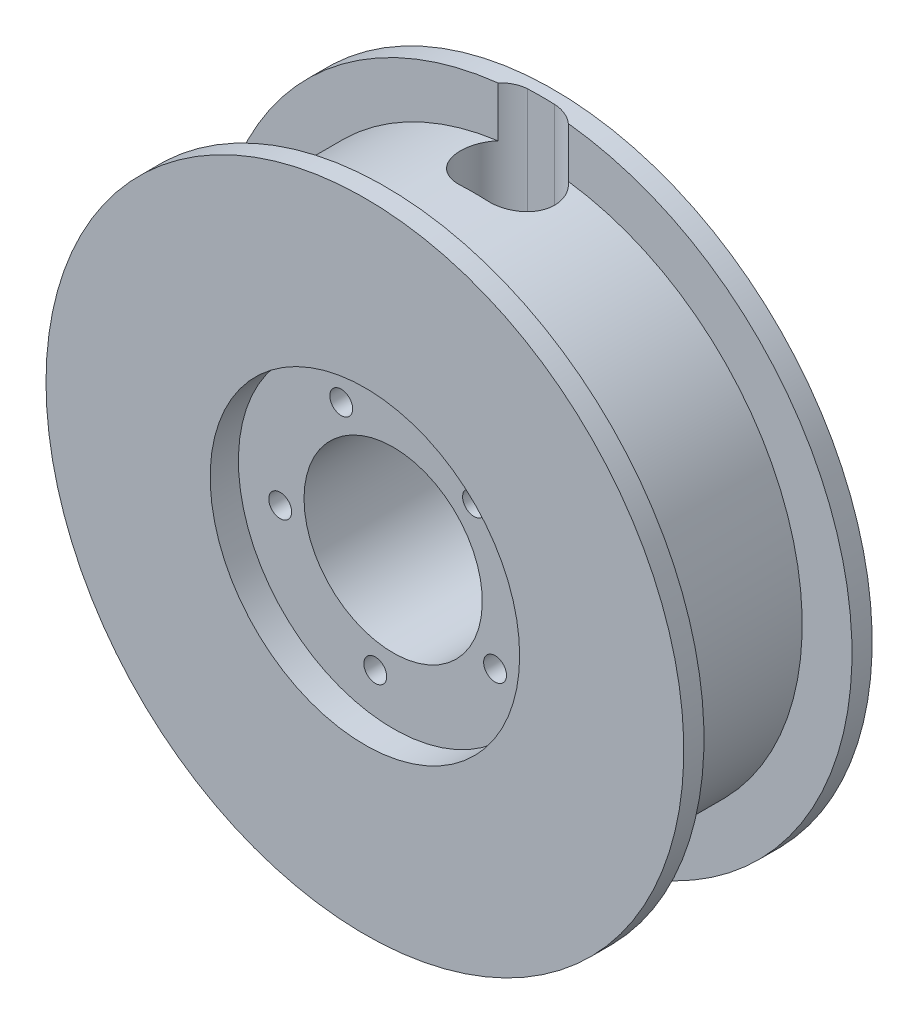
SolidWorks part; units mm, degrees
ref_plane "Ebene vorne" through (0, 0, 0) normal (0, 0, 1) x (1, 0, 0)
ref_plane "Ebene oben" through (0, 0, 0) normal (0, 1, 0) x (1, 0, 0)
ref_plane "Ebene rechts" through (0, 0, 0) normal (1, 0, 0) x (0, 0, -1)
sketch "Skizze3" plane through (0, 0, 0) normal (1, 0, 0) x (0, 0, -1)
  line L0 (-1.5, 4.2) -> (0, 4.2)
  line L1 (0, 4.2) -> (0, 0.5)
  line L2 (0, 0.5) -> (11, 0.5)
  line L3 (5.5, 0.5) -> (5.5, -39) construction
  line L4 (0, -39) -> (11, -39) construction
  line L5 (-1.5, 4.2) -> (-1.5, -12.875)
  line L6 (-1.5, -12.875) -> (12.5, -12.875)
  line L7 (12.5, 4.2) -> (12.5, -12.875)
  line L8 (11, 4.2) -> (11, 0.5)
  line L9 (12.5, 4.2) -> (11, 4.2)
  line L10 (11, 0) -> (0, 0) construction
  line L11 (13, -19.5) -> (-2, -19.5) construction
  line L12 (13, -47) -> (13, 8) construction
  line L13 (-2, 8) -> (-2, -47) construction
  line L14 (7.6, -13.375) -> (0.1, -13.375) construction
  point P10 (5.5, -12.875)
  dimension "D1" = 1.5
  dimension "D2" = 0.5
  dimension "D3" = 0.5
revolve "Rotation1" add sketch "Skizze3" angle 360 about L11
sketch "Skizze4" plane through (0, 0, 1.5) normal (0, 0, 1) x (1, 0, 0)
  circle A0 centre (0, -19.5) radius 11.5
  circle A1 centre (0, -19.5) radius 11 construction
  dimension "D1" = 0.5
extrude "Schnitt-Linear austragen1" cut sketch "Skizze4" against normal offset from surface (2.1 mm away) 0.5
sketch "Skizze5" plane through (0, 0, 1.5) normal (0, 0, 1) x (1, 0, 0)
  circle A0 centre (6.0104, -13.4896) radius 1
  circle A1 centre (7.5736, -23.3589) radius 1
  circle A2 centre (-1.3297, -27.8954) radius 1
  circle A3 centre (-8.3954, -20.8297) radius 1
  circle A4 centre (-3.8589, -11.9264) radius 1
  point P13 (0, -19.5)
  dimension "D2" = 2
  dimension "D1" = 5
extrude "Schnitt-Linear austragen2" cut sketch "Skizze5" against normal blind 1 from surface at -8
sketch "Skizze6" plane through (9.0133, -13.375, -16.4366) normal (0, 1, 0) x (1, 0, 0)
  line L0 (-10.0133, -7.3366) -> (-8.0133, -7.3366) construction
  line L1 (-10.0133, -4.8366) -> (-8.0133, -4.8366)
  line L2 (-10.0133, -9.8366) -> (-8.0133, -9.8366)
  arc A0 (-10.0133, -4.8366) -> (-10.0133, -9.8366) centre (-10.0133, -7.3366) ccw
  arc A1 (-8.0133, -9.8366) -> (-8.0133, -4.8366) centre (-8.0133, -7.3366) ccw
  point P2 (-9.0133, -7.3366)
  dimension "D1" = 2.5
  dimension "D2" = 2
extrude "Schnitt-Linear austragen3" cut sketch "Skizze6" against normal up to surface and the other way through all
sketch "Skizze7" plane through (0, 0, 1.5) normal (0, 0, 1) x (1, 0, 0)
  circle A0 centre (-3.8589, -11.9264) radius 0.85
  circle A1 centre (6.0104, -13.4896) radius 0.85
  circle A2 centre (7.5736, -23.3589) radius 0.85
  circle A3 centre (-1.3297, -27.8954) radius 0.85
  circle A4 centre (-8.3954, -20.8297) radius 0.85
  point P13 (0, -19.5)
  dimension "D1" = 1.7
  dimension "D2" = 5
extrude "Schnitt-Linear austragen4" cut sketch "Skizze7" against normal blind 10
